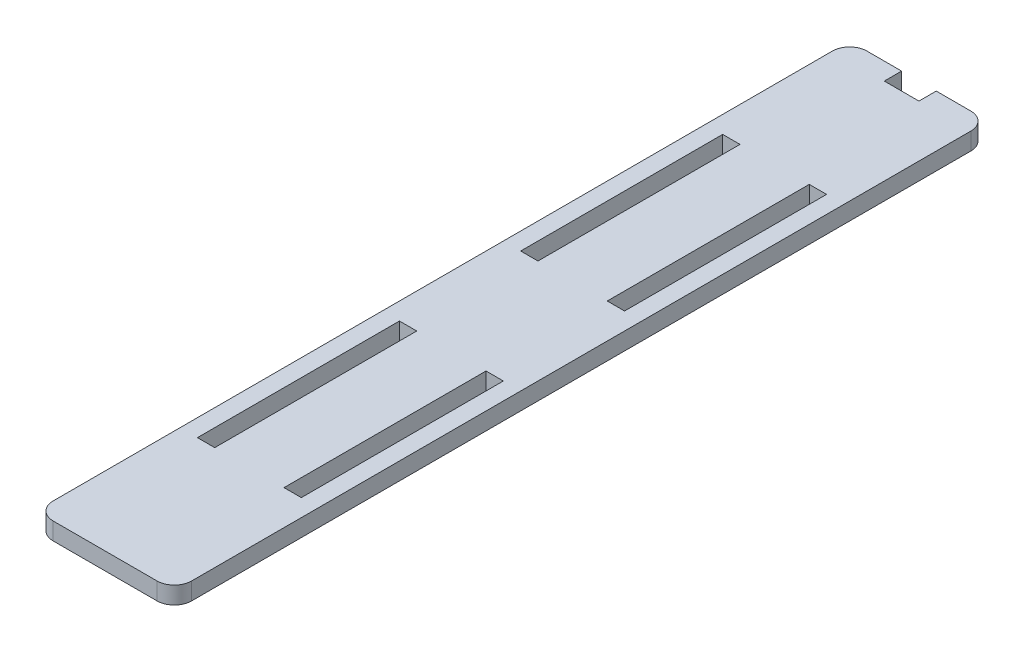
SolidWorks part; units mm, degrees
material "Acrylic (Medium-high impact)"
ref_plane "Plano frontal" through (0, 0, 0) normal (0, 0, 1) x (1, 0, 0)
ref_plane "Plano superior" through (0, 0, 0) normal (0, 1, 0) x (1, 0, 0)
ref_plane "Plano direito" through (0, 0, 0) normal (1, 0, 0) x (0, 0, -1)
sketch "Sketch1" plane through (0, 0, 0) normal (0, 1, 0) x (1, 0, 0)
  line L1 (-12, 70.5) -> (12, 70.5)
  line L2 (-12, 70.5) -> (-12, -70.5)
  line L3 (-12, -70.5) -> (12, -70.5)
  line L4 (12, 70.5) -> (12, -70.5)
  point P4 (0, 70.5)
  point P6 (-12, 0)
  dimension "D1" = 141
  dimension "D2" = 24
extrude "Boss-Extrude1" add sketch "Sketch1" along normal mid plane 3
sketch "Sketch2" plane through (0, 0, 0) normal (0, 1, 0) x (1, 0, 0)
  line L0 (12, 70.5) -> (-12, 70.5) construction
  line L1 (-9, 45.5) -> (-6, 45.5)
  line L2 (-9, 45.5) -> (-9, 10.5)
  line L3 (-9, 10.5) -> (-6, 10.5)
  line L4 (-6, 45.5) -> (-6, 10.5)
  line L5 (-12, 70.5) -> (-12, -70.5) construction
  line L6 (0, -1.65) -> (0, 1.65) construction
  line L7 (6, 45.5) -> (6, 10.5)
  line L8 (9, 10.5) -> (6, 10.5)
  line L9 (9, 45.5) -> (9, 10.5)
  line L10 (9, 45.5) -> (6, 45.5)
  line L21 (6, -10.5) -> (6, -45.5)
  line L22 (-9, -10.5) -> (-6, -10.5)
  line L23 (-9, -10.5) -> (-9, -45.5)
  line L24 (-9, -45.5) -> (-6, -45.5)
  line L25 (-6, -10.5) -> (-6, -45.5)
  line L26 (9, -45.5) -> (6, -45.5)
  line L27 (9, -10.5) -> (9, -45.5)
  line L28 (9, -10.5) -> (6, -10.5)
  line L29 (-12, -70.5) -> (12, -70.5) construction
  dimension "D1" = 3
  dimension "D2" = 35
  dimension "D3" = 25
  dimension "D4" = 3
  dimension "D5" = 21
  dimension "D6" = 25
extrude "Cut-Extrude1" cut sketch "Sketch2" against normal through all both and the other way through all
fillet "Fillet1" radius 3 4 edges at (12, 0, 70.5) (-12, 0, 70.5) (12, 0, -70.5) (-12, 0, -70.5)
sketch "Sketch3" plane through (0, 0, 0) normal (0, 1, 0) x (1, 0, 0)
  line L0 (9, 70.5) -> (-9, 70.5) construction
  line L1 (-3, 70.5) -> (3, 70.5)
  line L2 (-3, 70.5) -> (-3, 67.5)
  line L3 (-3, 67.5) -> (3, 67.5)
  line L4 (3, 70.5) -> (3, 67.5)
  point P6 (0, 67.5)
  dimension "D1" = 3
  dimension "D2" = 6
extrude "Cut-Extrude2" cut sketch "Sketch3" against normal through all both and the other way through all
